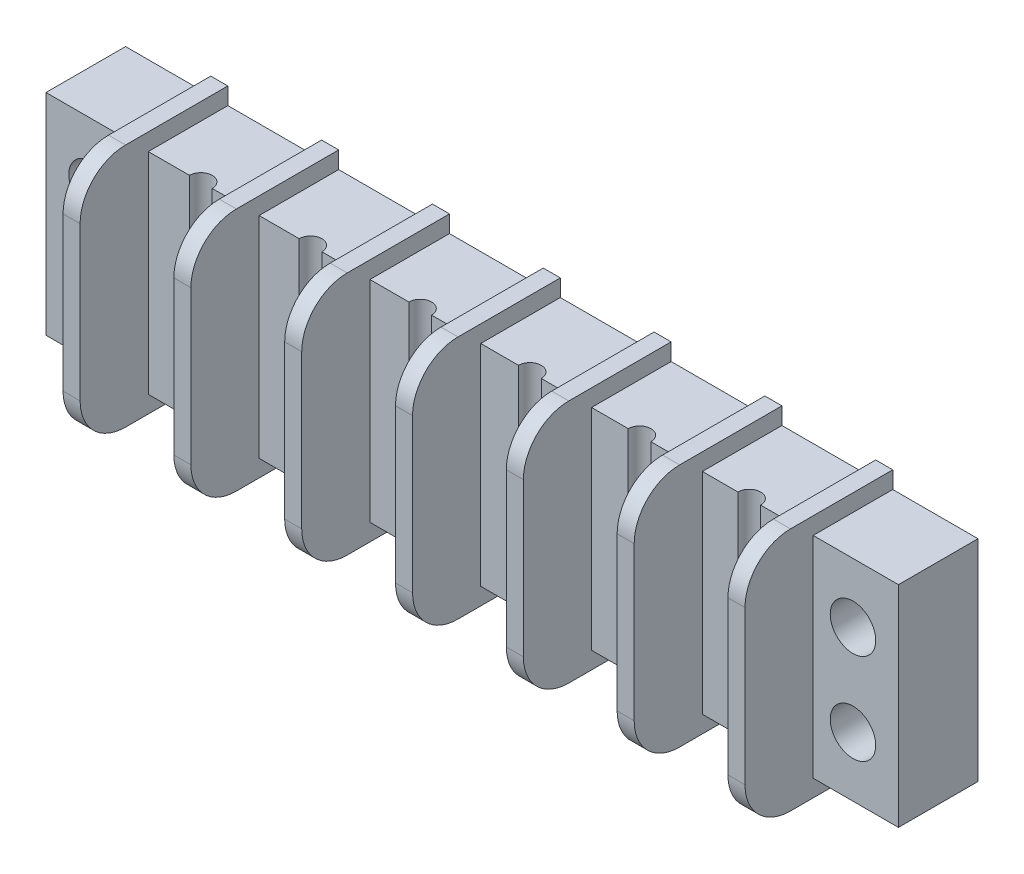
SolidWorks part; units mm, degrees
ref_plane "Plan de face" through (0, 0, 0) normal (0, 0, 1) x (1, 0, 0)
ref_plane "Plan de dessus" through (0, 0, 0) normal (0, 1, 0) x (1, 0, 0)
ref_plane "Plan de droite" through (0, 0, 0) normal (1, 0, 0) x (0, 0, -1)
sketch "Esquisse1" plane through (0, 0, 0) normal (0, 0, 1) x (1, 0, 0)
  line L1 (-29.2453, 13.0896) -> (45.7547, 13.0896)
  line L2 (-29.2453, 13.0896) -> (-29.2453, -5.4104)
  line L3 (-29.2453, -5.4104) -> (45.7547, -5.4104)
  line L4 (45.7547, 13.0896) -> (45.7547, -5.4104)
  dimension "D1" = 75
  dimension "D2" = 18.5
extrude "Boss.-Extru.1" add sketch "Esquisse1" along normal blind 7
sketch "Esquisse2" plane through (0, 0, 0) normal (0, 0, -1) x (-1, 0, 0)
  line L0 (-45.7547, 3.8396) -> (29.2453, 3.8396) construction
  line L1 (-45.7547, -5.4104) -> (-45.7547, 13.0896) construction
  line L2 (29.2453, 13.0896) -> (29.2453, -5.4104) construction
  line L3 (-8.2547, 13.0896) -> (-8.2547, -5.4104) construction
  line L4 (-45.7547, 13.0896) -> (29.2453, 13.0896) construction
  line L5 (29.2453, -5.4104) -> (-45.7547, -5.4104) construction
  circle A0 centre (-41.7547, 7.8396) radius 2
  circle A1 centre (-41.7547, -0.1604) radius 2
  circle A2 centre (25.2453, -0.1604) radius 2
  circle A3 centre (25.2453, 7.8396) radius 2
  dimension "D1" = 4
  dimension "D2" = 4
  dimension "D3" = 33.5
extrude "Enlèv. mat.-Extru.1" cut sketch "Esquisse2" against normal up to next
sketch "Esquisse3" plane through (0, 0, 0) normal (0, 0, -1) x (-1, 0, 0)
  line L0 (-45.7547, 3.8396) -> (29.2453, 3.8396) construction
  line L1 (-38.2547, -6.9104) -> (-36.7547, -6.9104)
  line L2 (-38.2547, -6.9104) -> (-38.2547, 14.5896)
  line L3 (-38.2547, 14.5896) -> (-36.7547, 14.5896)
  line L4 (-36.7547, -6.9104) -> (-36.7547, 14.5896)
  line L5 (-45.7547, -5.4104) -> (-45.7547, 13.0896) construction
  line L6 (29.2453, 13.0896) -> (29.2453, -5.4104) construction
  line L7 (-28.5047, -6.9104) -> (-28.5047, 14.5896)
  line L8 (-28.5047, -6.9104) -> (-27.0047, -6.9104)
  line L9 (-27.0047, -6.9104) -> (-27.0047, 14.5896)
  line L10 (-28.5047, 14.5896) -> (-27.0047, 14.5896)
  line L11 (-18.7547, -6.9104) -> (-18.7547, 14.5896)
  line L12 (-18.7547, -6.9104) -> (-17.2547, -6.9104)
  line L13 (-17.2547, -6.9104) -> (-17.2547, 14.5896)
  line L14 (-18.7547, 14.5896) -> (-17.2547, 14.5896)
  line L15 (-9.0047, -6.9104) -> (-9.0047, 14.5896)
  line L16 (-9.0047, -6.9104) -> (-7.5047, -6.9104)
  line L17 (-7.5047, -6.9104) -> (-7.5047, 14.5896)
  line L18 (-9.0047, 14.5896) -> (-7.5047, 14.5896)
  line L19 (0.7453, -6.9104) -> (0.7453, 14.5896)
  line L20 (0.7453, -6.9104) -> (2.2453, -6.9104)
  line L21 (2.2453, -6.9104) -> (2.2453, 14.5896)
  line L22 (0.7453, 14.5896) -> (2.2453, 14.5896)
  line L23 (10.4953, -6.9104) -> (10.4953, 14.5896)
  line L24 (10.4953, -6.9104) -> (11.9953, -6.9104)
  line L25 (11.9953, -6.9104) -> (11.9953, 14.5896)
  line L26 (10.4953, 14.5896) -> (11.9953, 14.5896)
  line L27 (20.2453, -6.9104) -> (20.2453, 14.5896)
  line L28 (20.2453, -6.9104) -> (21.7453, -6.9104)
  line L29 (21.7453, -6.9104) -> (21.7453, 14.5896)
  line L30 (20.2453, 14.5896) -> (21.7453, 14.5896)
  dimension "D1" = 1.5
  dimension "D2" = 21.5
  dimension "D3" = 10.75
  dimension "D4" = 7.5
  dimension "D5" = 7
  dimension "D6" = 7.5
extrude "Boss.-Extru.2" add sketch "Esquisse3" against normal blind 13
fillet "Congé1" radius 4 14 edges at (-20.9953, -6.9104, 13) (-11.2453, -6.9104, 13) (-1.4953, -6.9104, 13) (8.2547, -6.9104, 13) (18.0047, -6.9104, 13) (27.7547, -6.9104, 13) (37.5047, -6.9104, 13) (-20.9953, 14.5896, 13) (-11.2453, 14.5896, 13) (-1.4953, 14.5896, 13) (8.2547, 14.5896, 13) (18.0047, 14.5896, 13) (27.7547, 14.5896, 13) (37.5047, 14.5896, 13)
sketch "Esquisse4" plane through (0, -5.4104, 0) normal (0, -1, 0) x (1, 0, 0)
  line L0 (28.5047, 7) -> (36.7547, 7) construction
  circle A0 centre (32.6297, 7) radius 1
  dimension "D1" = 2
extrude "Enlèv. mat.-Extru.2" cut sketch "Esquisse4" against normal up to next (18.5 mm away)
pattern_linear "Répétition linéaire1" count 6 spacing 9.65 along (-1, 0, 0) of "Enlèv. mat.-Extru.2"
